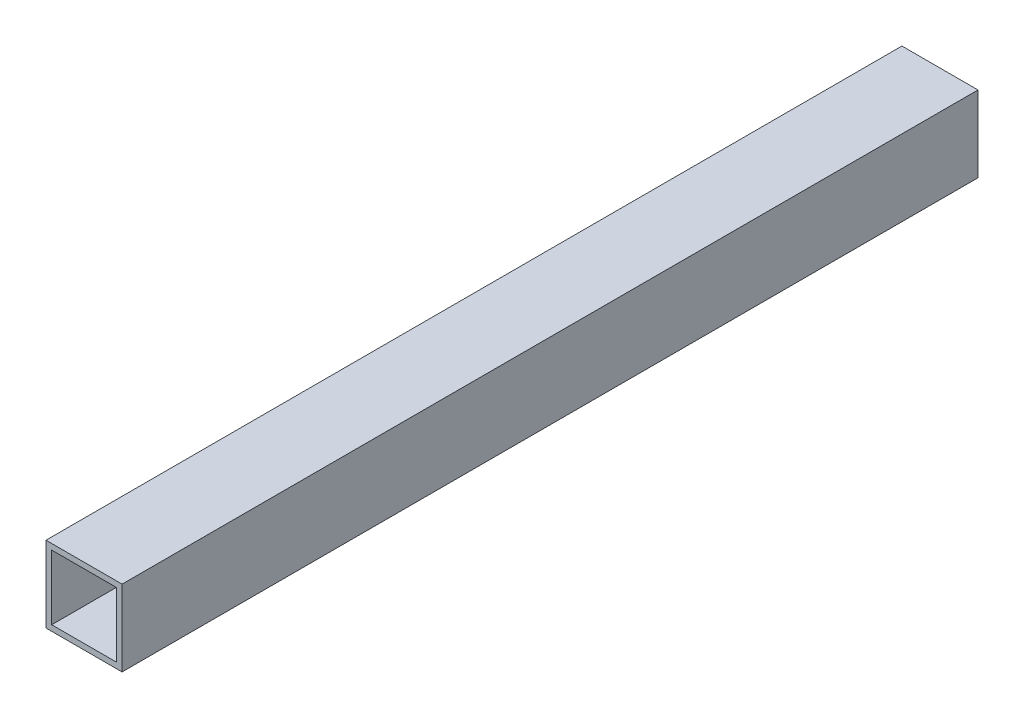
SolidWorks part; units mm, degrees
ref_plane "Front Plane" through (0, 0, 0) normal (0, 0, 1) x (1, 0, 0)
ref_plane "Top Plane" through (0, 0, 0) normal (0, 1, 0) x (1, 0, 0)
ref_plane "Right Plane" through (0, 0, 0) normal (1, 0, 0) x (0, 0, -1)
sketch "Sketch1" plane through (0, 0, 0) normal (0, 0, 1) x (1, 0, 0)
  line L0 (17, 17) -> (-17, 17)
  line L1 (20, -20) -> (-20, -20)
  line L2 (20, -20) -> (20, 20)
  line L3 (20, 20) -> (-20, 20)
  line L4 (-20, -20) -> (-20, 20)
  line L5 (20, -20) -> (-20, 20) construction
  line L6 (20, 20) -> (-20, -20) construction
  line L7 (-17, -17) -> (-17, 17)
  line L8 (17, -17) -> (-17, -17)
  line L9 (17, -17) -> (17, 17)
  point P0 (0, 0)
  dimension "D1" = 40
  dimension "D2" = 40
  dimension "D3" = 3
extrude "Boss-Extrude1" add sketch "Sketch1" along normal blind 450
